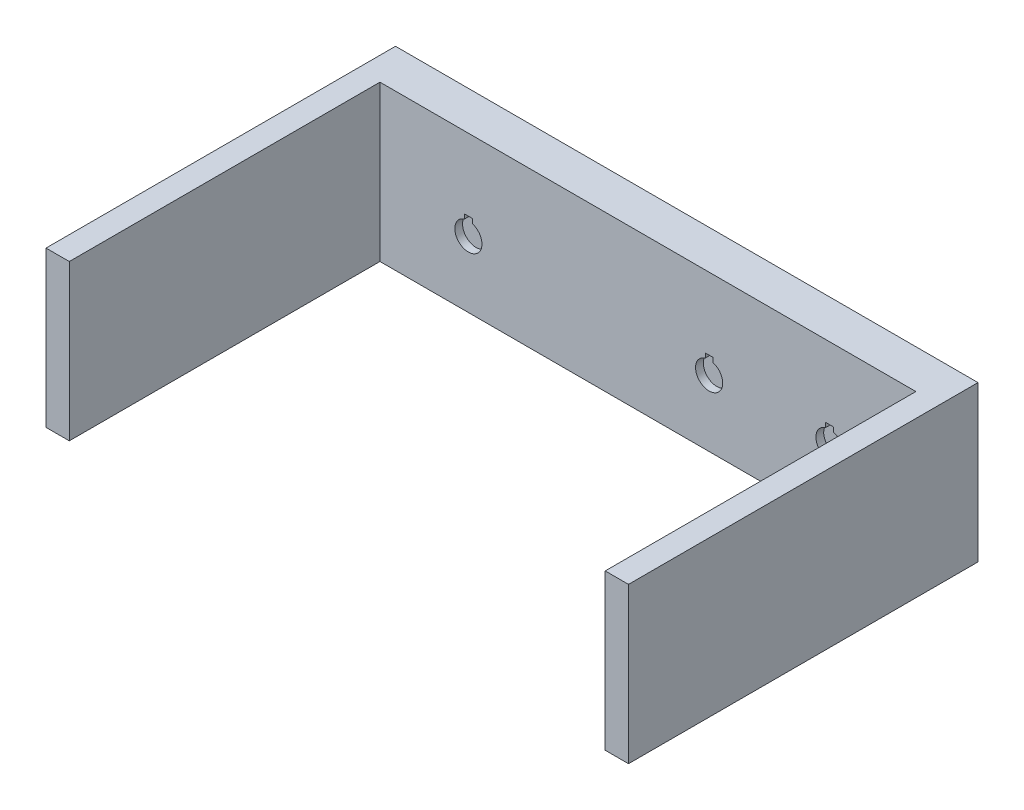
SolidWorks part; units mm, degrees
ref_plane "Front Plane" through (0, 0, 0) normal (0, 0, 1) x (1, 0, 0)
ref_plane "Top Plane" through (0, 0, 0) normal (0, 1, 0) x (1, 0, 0)
ref_plane "Right Plane" through (0, 0, 0) normal (1, 0, 0) x (0, 0, -1)
sketch "Sketch1" plane through (0, 0, 0) normal (0, 0, 1) x (1, 0, 0)
  line L1 (75, -20) -> (-75, -20)
  line L2 (75, -20) -> (75, 20)
  line L3 (75, 20) -> (-75, 20)
  line L4 (-75, -20) -> (-75, 20)
  point P0 (0, 0)
  dimension "D1" = 150
  dimension "D2" = 40
extrude "Boss-Extrude1" add sketch "Sketch1" along normal blind 10
sketch "Sketch2" plane through (0, -20, 0) normal (0, -1, 0) x (1, 0, 0)
  line L0 (75, 10) -> (75, 0) construction
  line L1 (65.2658, 2) -> (-64.7342, 2)
  line L2 (65.2658, 2) -> (65.2658, 8)
  line L3 (65.2658, 8) -> (-64.7342, 8)
  line L4 (-64.7342, 2) -> (-64.7342, 8)
  line L5 (65.2658, 2) -> (-64.7342, 8) construction
  line L6 (65.2658, 8) -> (-64.7342, 2) construction
  point P0 (0.2658, 5)
  point P8 (75, 5)
  dimension "D1" = 130
  dimension "D2" = 6
extrude "Cut-Extrude1" cut sketch "Sketch2" against normal blind 34
sketch "Sketch3" plane through (0, 0, 10) normal (0, 0, 1) x (1, 0, 0)
  line L1 (64.7658, -19.75) -> (-64.2342, -19.75)
  line L2 (64.7658, -19.75) -> (64.7658, 13.75)
  line L3 (64.7658, 13.75) -> (-64.2342, 13.75)
  line L4 (-64.2342, -19.75) -> (-64.2342, 13.75)
  line L6 (65.2658, 14) -> (-64.7342, 14) construction
  line L8 (-64.7342, 14) -> (-64.7342, -20) construction
  line L9 (65.2658, 14) -> (65.2658, -20) construction
  line L10 (-46.2342, -3) -> (46.7658, -3) construction
  line L11 (16.7658, 1.5041) -> (16.7658, 0.3541)
  line L12 (16.7658, 1.5041) -> (14.7658, 1.5041)
  line L13 (-45.2342, 1.5041) -> (-47.2342, 1.5041)
  line L14 (-45.2342, 1.5041) -> (-45.2342, 0.3541)
  line L16 (-47.2342, 1.5041) -> (-47.2342, 0.3541)
  line L17 (14.7658, 1.5041) -> (14.7658, 0.3541)
  line L18 (47.7658, 1.5041) -> (47.7658, 0.3541)
  line L19 (47.7658, 1.5041) -> (45.7658, 1.5041)
  line L20 (45.7658, 1.5041) -> (45.7658, 0.3541)
  line L21 (-16.2342, 1.5041) -> (-16.2342, 0.3541) [skipped]
  line L22 (-14.2342, 1.5041) -> (-14.2342, 0.3541) [skipped]
  line L23 (-14.2342, 1.5041) -> (-16.2342, 1.5041) [skipped]
  arc A0 (-47.2342, 0.3541) -> (-45.2342, 0.3541) centre (-46.2342, -3) ccw
  arc A2 (14.7658, 0.3541) -> (16.7658, 0.3541) centre (15.7658, -3) ccw
  arc A3 (45.7658, 0.3541) -> (47.7658, 0.3541) centre (46.7658, -3) ccw
  arc A4 (-18.7342, -3) -> (-11.7342, -3) centre (-15.2342, -3) ccw [skipped]
  arc A5 (-16.2342, 0.3541) -> (-14.2342, 0.3541) centre (-15.2342, -3) ccw
  point P0 (0, 0)
  point P14 (-64.2342, -3)
  point P15 (0.2658, -3)
  point P16 (0.2658, 13.75)
  dimension "D6" = 7
  dimension "D1" = 33.5
  dimension "D2" = 0.25
  dimension "D3" = 0.5
  dimension "D4" = 0.5
  dimension "D5" = 93
  dimension "D7" = 1.15
  dimension "D8" = 4
  dimension "D9" = 2
extrude "Cut-Extrude3" cut sketch "Sketch3" against normal blind 10 contours A0 L14 L13 L16 | L11 A2 L17 L12 | L18 A3 L20 L19
sketch "Sketch4" plane through (0, 0, 0) normal (0, 0, -1) x (-1, 0, 0)
  line L0 (-47.7658, 0.3541) -> (-47.7658, 1.5041)
  line L1 (-47.7658, 1.5041) -> (-45.7658, 1.5041)
  line L2 (-45.7658, 1.5041) -> (-45.7658, 0.3541)
  line L3 (-14.7658, 1.5041) -> (-14.7658, 0.3541)
  line L4 (-16.7658, 0.3541) -> (-16.7658, 1.5041)
  line L5 (-16.7658, 1.5041) -> (-14.7658, 1.5041)
  line L9 (47.2342, 1.5041) -> (47.2342, 0.3541)
  line L10 (45.2342, 0.3541) -> (45.2342, 1.5041)
  line L11 (45.2342, 1.5041) -> (47.2342, 1.5041)
  line L12 (14.2342, 0.3541) -> (14.2342, 1.5041)
  line L13 (14.2342, 1.5041) -> (16.2342, 1.5041)
  line L14 (16.2342, 1.5041) -> (16.2342, 0.3541)
  arc A0 (-47.7658, 0.3541) -> (-45.7658, 0.3541) centre (-46.7658, -3) cw
  arc A1 (-16.7658, 0.3541) -> (-14.7658, 0.3541) centre (-15.7658, -3) cw
  arc A3 (45.2342, 0.3541) -> (47.2342, 0.3541) centre (46.2342, -3) cw
  arc A4 (14.2342, 0.3541) -> (16.2342, 0.3541) centre (15.2342, -3) cw
  dimension "D1" = 4
extrude "Boss-Extrude2" add sketch "Sketch4" against normal blind 2 contours L2 A0 L0 L1 | L3 A1 L4 L5 | L9 A3 L10 L11
sketch "Sketch5" plane through (0, 0, 10) normal (0, 0, 1) x (1, 0, 0)
  line L0 (-75, -20) -> (75, -20) construction
  line L1 (-75, 20) -> (-69, 20)
  line L2 (-75, 20) -> (-75, -20)
  line L3 (-75, -20) -> (-69, -20)
  line L4 (-69, 20) -> (-69, -20)
  line L6 (75, 20) -> (69, 20)
  line L7 (75, 20) -> (75, -20)
  line L8 (75, -20) -> (69, -20)
  line L9 (69, 20) -> (69, -20)
  dimension "D1" = 6
  dimension "D2" = 6
extrude "Boss-Extrude3" add sketch "Sketch5" along normal blind 80
